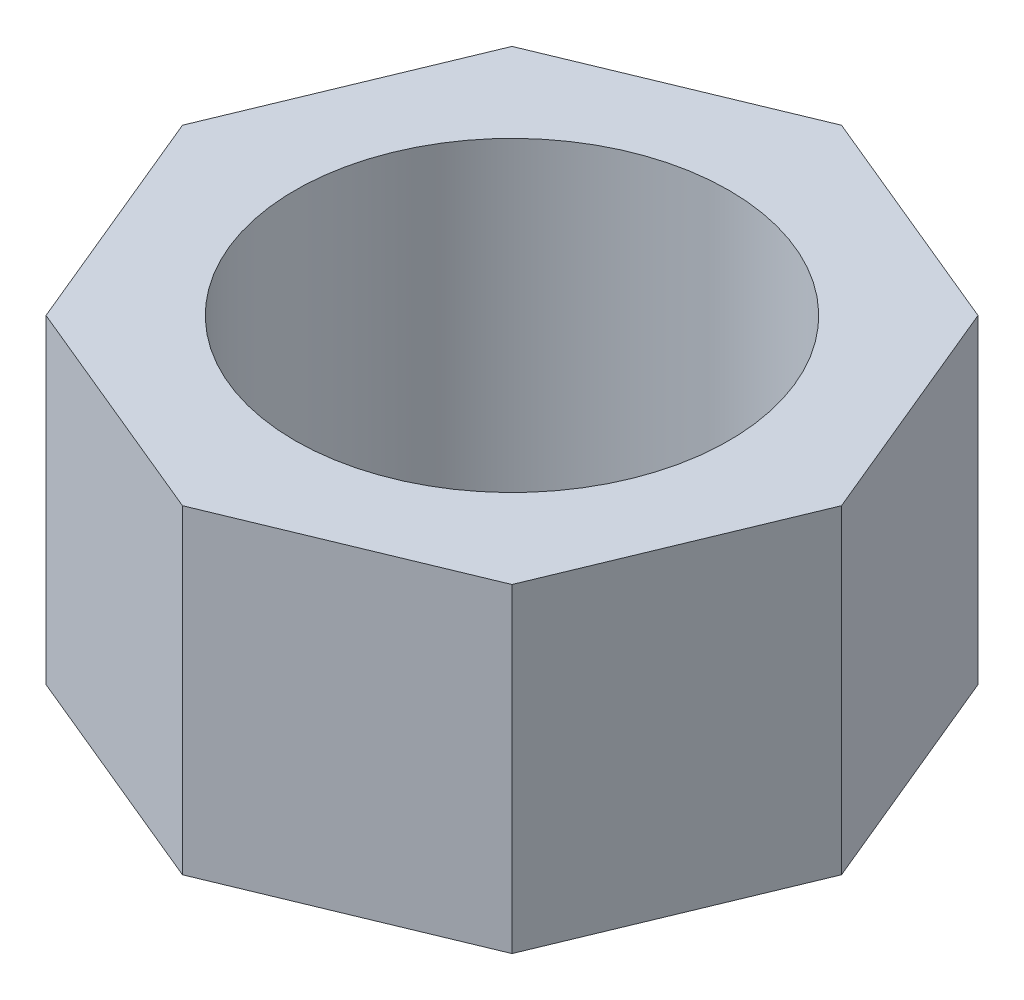
SolidWorks part; units mm, degrees
ref_plane "Front Plane" through (0, 0, 0) normal (0, 0, 1) x (1, 0, 0)
ref_plane "Top Plane" through (0, 0, 0) normal (0, 1, 0) x (1, 0, 0)
ref_plane "Right Plane" through (0, 0, 0) normal (1, 0, 0) x (0, 0, -1)
sketch "Sketch1" plane through (0, 0, 0) normal (0, 1, 0) x (1, 0, 0)
  line L1 (0, 8.6591) -> (-6.1229, 6.1229)
  line L2 (-6.1229, 6.1229) -> (-8.6591, 0)
  line L3 (-8.6591, 0) -> (-6.1229, -6.1229)
  line L4 (-6.1229, -6.1229) -> (0, -8.6591)
  line L5 (0, -8.6591) -> (6.1229, -6.1229)
  line L6 (6.1229, -6.1229) -> (8.6591, 0)
  line L7 (8.6591, 0) -> (6.1229, 6.1229)
  line L8 (6.1229, 6.1229) -> (0, 8.6591)
  circle A0 centre (0, 0) radius 8 construction
  circle A1 centre (0, 0) radius 5.7
  dimension "D1" = 16
  dimension "D2" = 11.4
extrude "Boss-Extrude1" add sketch "Sketch1" along normal blind 8.4 contours L7 L8 L1 L2 L3 L4 L5 L6 A1
cosmetic thread "Cosmetic Thread1"
